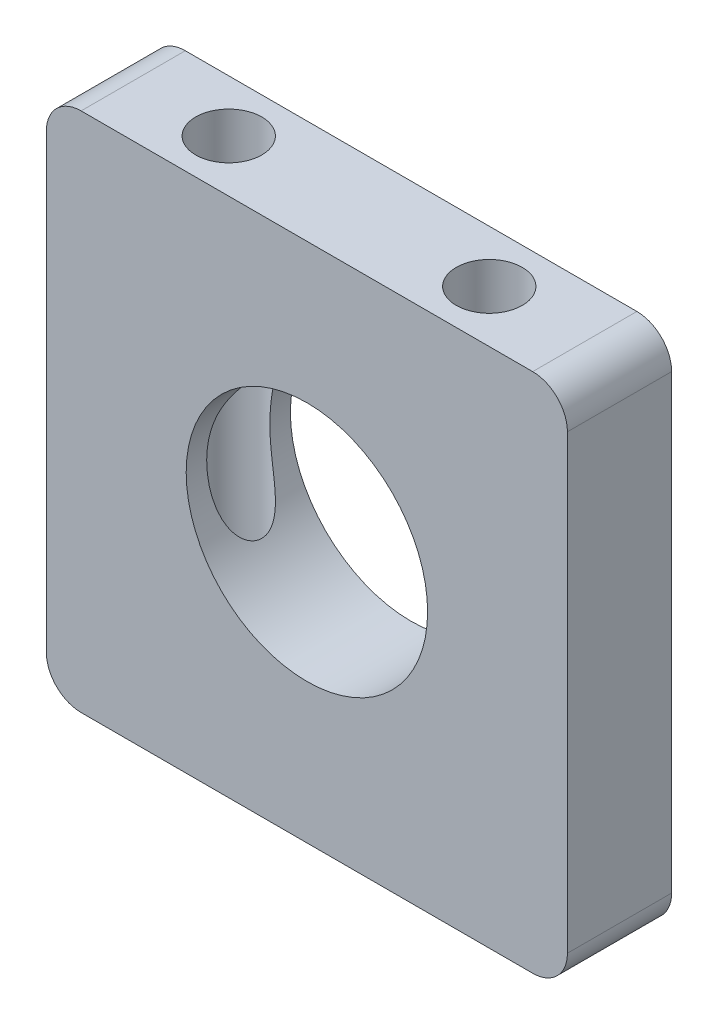
SolidWorks part; units mm, degrees
ref_plane "Front Plane" through (0, 0, 0) normal (0, 0, 1) x (1, 0, 0)
ref_plane "Top Plane" through (0, 0, 0) normal (0, 1, 0) x (1, 0, 0)
ref_plane "Right Plane" through (0, 0, 0) normal (1, 0, 0) x (0, 0, -1)
sketch "Sketch1" plane through (0, 0, 0) normal (0, 0, 1) x (1, 0, 0)
  line L1 (19.05, -19.05) -> (-19.05, -19.05)
  line L2 (19.05, -19.05) -> (19.05, 19.05)
  line L3 (19.05, 19.05) -> (-19.05, 19.05)
  line L4 (-19.05, -19.05) -> (-19.05, 19.05)
  line L5 (19.05, -19.05) -> (-19.05, 19.05) construction
  line L6 (19.05, 19.05) -> (-19.05, -19.05) construction
  circle A0 centre (0, 0) radius 8.8265
  point P0 (0, 0)
  dimension "D2" = 17.653
  dimension "D1" = 38.1
extrude "Boss-Extrude1" add sketch "Sketch1" along normal blind 7.62
fillet "Fillet1" radius 2.54 4 edges at (19.05, -19.05, 3.81) (-19.05, -19.05, 3.81) (-19.05, 19.05, 3.81) (19.05, 19.05, 3.81)
sketch "Sketch2" plane through (0, -19.05, 0) normal (0, -1, 0) x (1, 0, 0)
  line L0 (-16.51, 7.62) -> (-19.05, 7.62) construction
  line L1 (-19.05, 7.62) -> (-19.05, 0) construction
  line L2 (-19.05, 0) -> (-16.51, 0) construction
  line L3 (19.05, 7.62) -> (16.51, 7.62) construction
  line L4 (16.51, 0) -> (19.05, 0) construction
  line L5 (19.05, 0) -> (19.05, 7.62) construction
  line L6 (-16.51, 0) -> (16.51, 0) construction
  line L7 (16.51, 7.62) -> (-16.51, 7.62) construction
  line L8 (-16.51, 7.62) -> (-19.05, 7.62)
  line L9 (-19.05, 7.62) -> (-19.05, 0)
  line L10 (-19.05, 0) -> (-16.51, 0)
  line L11 (19.05, 7.62) -> (16.51, 7.62)
  line L12 (16.51, 0) -> (19.05, 0)
  line L13 (19.05, 0) -> (19.05, 7.62)
  line L14 (-16.51, 0) -> (16.51, 0)
  line L15 (16.51, 7.62) -> (-16.51, 7.62)
  line L16 (0, 0) -> (0, 7.62) construction
  line L17 (-9.525, 3.81) -> (9.525, 3.81) construction
  circle A0 centre (9.525, 3.81) radius 2.413
  circle A1 centre (-9.525, 3.81) radius 2.413
  point P14 (0, 3.81)
  point P16 (0, 3.81)
  dimension "D1" = 4.826
  dimension "D2" = 9.525
  dimension "D4" = 3.81
  dimension "D5" = 3.81
extrude "Cut-Extrude1" cut sketch "Sketch2" against normal blind 7.62 contours A0 | A1
sketch "Sketch3" plane through (0, 19.05, 0) normal (0, 1, 0) x (1, 0, 0)
  line L0 (16.51, -7.62) -> (19.05, -7.62) construction
  line L1 (19.05, -7.62) -> (19.05, 0) construction
  line L2 (19.05, 0) -> (16.51, 0) construction
  line L3 (-19.05, -7.62) -> (-16.51, -7.62) construction
  line L4 (-16.51, 0) -> (-19.05, 0) construction
  line L5 (-19.05, 0) -> (-19.05, -7.62) construction
  line L6 (16.51, 0) -> (-16.51, 0) construction
  line L7 (-16.51, -7.62) -> (16.51, -7.62) construction
  line L8 (16.51, -7.62) -> (19.05, -7.62)
  line L9 (19.05, -7.62) -> (19.05, 0)
  line L10 (19.05, 0) -> (16.51, 0)
  line L11 (-19.05, -7.62) -> (-16.51, -7.62)
  line L12 (-16.51, 0) -> (-19.05, 0)
  line L13 (-19.05, 0) -> (-19.05, -7.62)
  line L14 (16.51, 0) -> (-16.51, 0)
  line L15 (-16.51, -7.62) -> (16.51, -7.62)
  line L16 (0, 0) -> (0, -7.62) construction
  line L17 (0, -3.81) -> (9.525, -3.81) construction
  line L18 (0, -3.81) -> (-9.525, -3.81) construction
  circle A0 centre (-9.525, -3.81) radius 2.413
  circle A1 centre (9.525, -3.81) radius 2.413
  dimension "D5" = 4.826
  dimension "D1" = 9.525
  dimension "D2" = 3.81
  dimension "D4" = 3.81
extrude "Cut-Extrude2" cut sketch "Sketch3" against normal blind 7.62 contours A0 | A1
sketch "Sketch4" plane through (0, 19.05, 0) normal (0, 1, 0) x (1, 0, 0)
  circle A0 centre (9.525, -3.81) radius 2.413 construction
  circle A1 centre (9.525, -3.81) radius 2.413
  circle A2 centre (-9.525, -3.81) radius 2.413 construction
  circle A3 centre (-9.525, -3.81) radius 2.413
extrude "Cut-Extrude3" cut sketch "Sketch4" against normal through all
